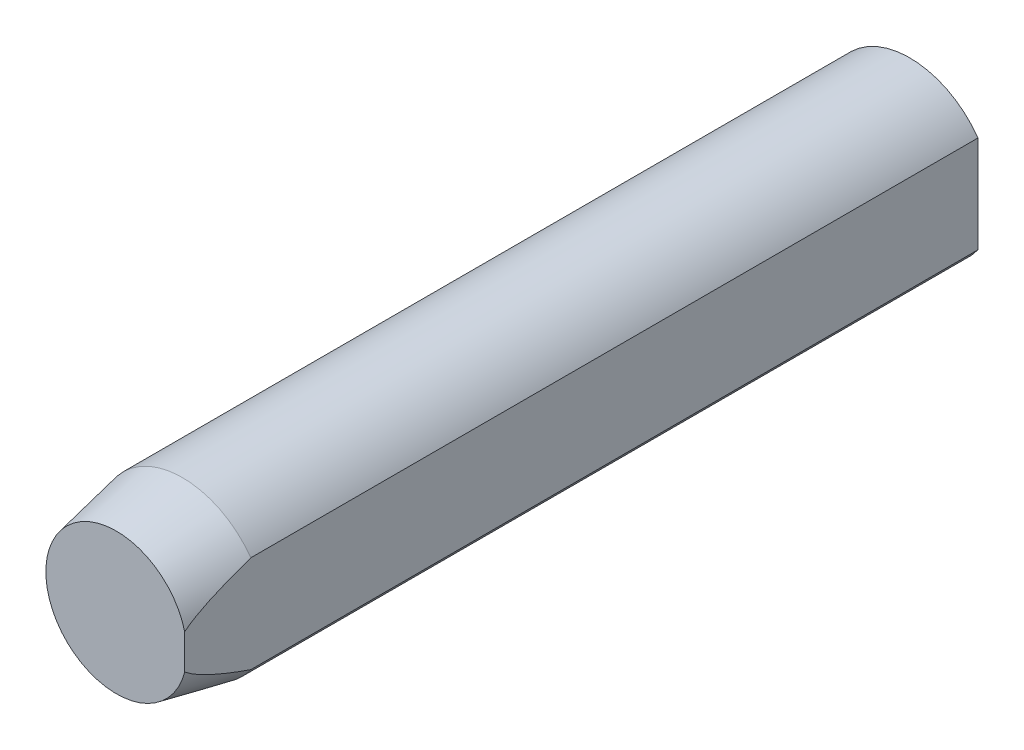
SolidWorks part; units mm, degrees
ref_plane "前视基准面" through (0, 0, 0) normal (0, 0, 1) x (1, 0, 0)
ref_plane "上视基准面" through (0, 0, 0) normal (0, 1, 0) x (1, 0, 0)
ref_plane "右视基准面" through (0, 0, 0) normal (1, 0, 0) x (0, 0, -1)
sketch "草图1" plane through (0, 0, 0) normal (0, 0, 1) x (1, 0, 0)
  circle A0 centre (0, 0) radius 1.9
  dimension "D1" = 3.8
extrude "凸台-拉伸1" add sketch "草图1" along normal blind 18
chamfer "倒角1" distance 1.5 distance2 0.3 1 edges at (1.9, 0, 18)
sketch "草图2" plane through (0, 0, 0) normal (0, 0, -1) x (-1, 0, 0)
  line L1 (-1.55, -1.6681) -> (-2.25, -1.6681)
  line L2 (-1.55, -1.6681) -> (-1.55, 1.6681)
  line L3 (-1.55, 1.6681) -> (-2.25, 1.6681)
  line L4 (-2.25, -1.6681) -> (-2.25, 1.6681)
  line L5 (-1.55, -1.6681) -> (-2.25, 1.6681) construction
  line L6 (-1.55, 1.6681) -> (-2.25, -1.6681) construction
  circle A0 centre (0, 0) radius 1.9 construction
  point P0 (-1.9, 0)
  dimension "D1" = 0.7
extrude "切除-拉伸1" cut sketch "草图2" against normal blind 18
